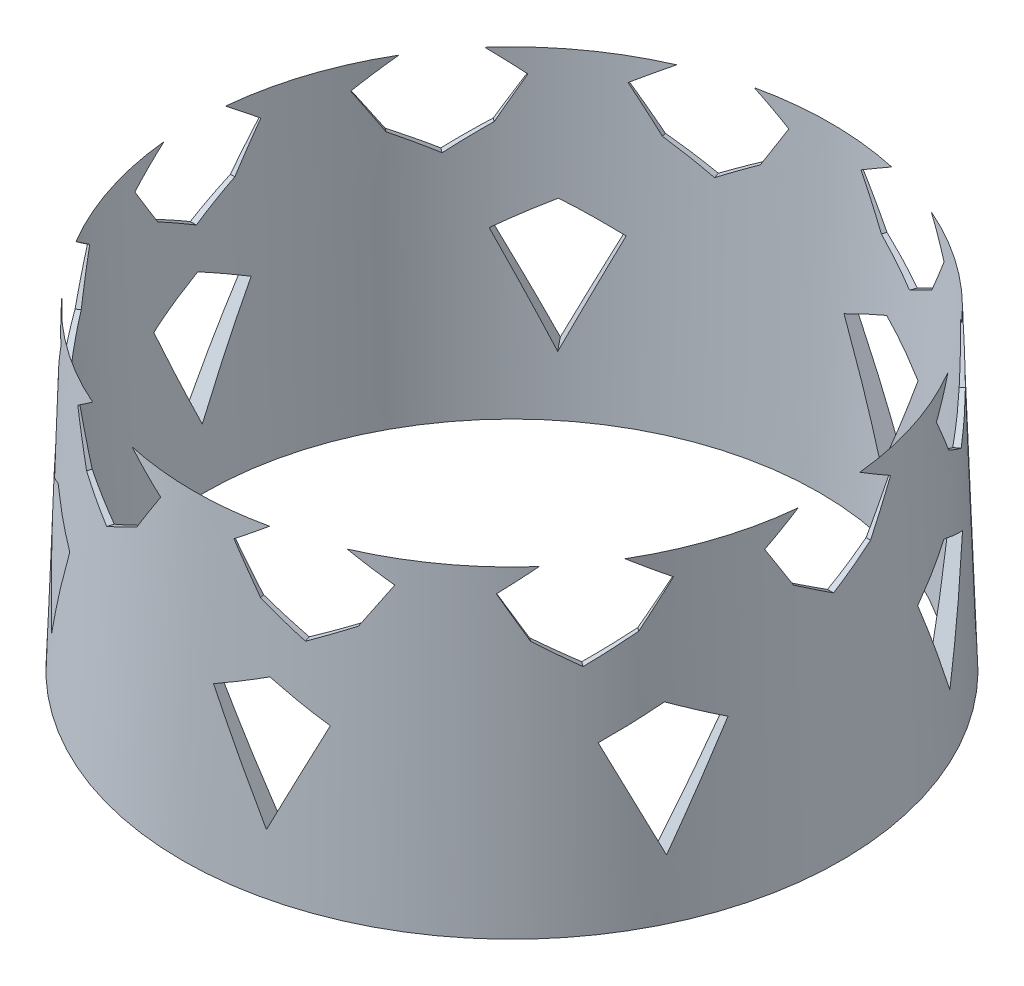
SolidWorks part; units mm, degrees
ref_plane "Front Plane" through (0, 0, 0) normal (0, 0, 1) x (1, 0, 0)
ref_plane "Top Plane" through (0, 0, 0) normal (0, 1, 0) x (1, 0, 0)
ref_plane "Right Plane" through (0, 0, 0) normal (1, 0, 0) x (0, 0, -1)
sketch "Sketch1" plane through (0, 0, 0) normal (0, 1, 0) x (1, 0, 0)
  circle A0 centre (0, 0) radius 37.5
  circle A1 centre (0, 0) radius 35
  dimension "D1" = 75
  dimension "D2" = 70
extrude "Boss-Extrude1" add sketch "Sketch1" along normal blind 40 draft 2
sketch "Sketch2" plane through (0, 0, 0) normal (1, 0, 0) x (0, 0, -1)
  line L0 (-36.25, 35.7953) -> (36.25, 35.7953) construction
  line L1 (-3.5, 35.7953) -> (-7.5347, 33.2021)
  line L2 (-7.5347, 33.2021) -> (-4.594, 28.6266)
  line L3 (-4.594, 28.6266) -> (0, 25.9144)
  line L4 (0, 25.9144) -> (4.22, 28.6266)
  line L5 (4.22, 28.6266) -> (6.9213, 33.2021)
  line L6 (6.9213, 33.2021) -> (3.5, 35.7953)
  arc A0 (3.5, 35.7953) -> (-3.5, 35.7953) centre (0, 35.7953) ccw
  dimension "D1" = 7
extrude "Cut-Extrude1" cut sketch "Sketch2" against normal blind 40
pattern_circular "CirPattern1" count 10 every 36 about axis through (0, 0, 0) along (0, 1, 0) of "Cut-Extrude1"
sketch "Sketch3" plane through (0, 0, 0) normal (1, 0, 0) x (0, 0, -1)
  line L0 (0, 21.3786) -> (-5.5418, 18.4429)
  line L1 (-5.5418, 18.4429) -> (0, 6.6364)
  line L2 (0, 21.3786) -> (5.5418, 18.4429)
  line L3 (5.5418, 18.4429) -> (0, 6.6364)
  line L4 (0, 0) -> (0, 33.2021) construction
  point P2 (-10.7215, 13.4918)
  point P4 (0, 10.483)
  point P8 (11.4063, 12.3492)
  point P9 (0, 0)
  point P10 (0, 8.2741)
  point P12 (-5.5418, 18.4429)
  point P13 (0, 6.6364)
extrude "Cut-Extrude2" cut sketch "Sketch3" against normal blind 40
pattern_circular "CirPattern2" count 7 every 51.5 about axis through (0, 0, 0) along (0, 1, 0) of "Cut-Extrude2"
